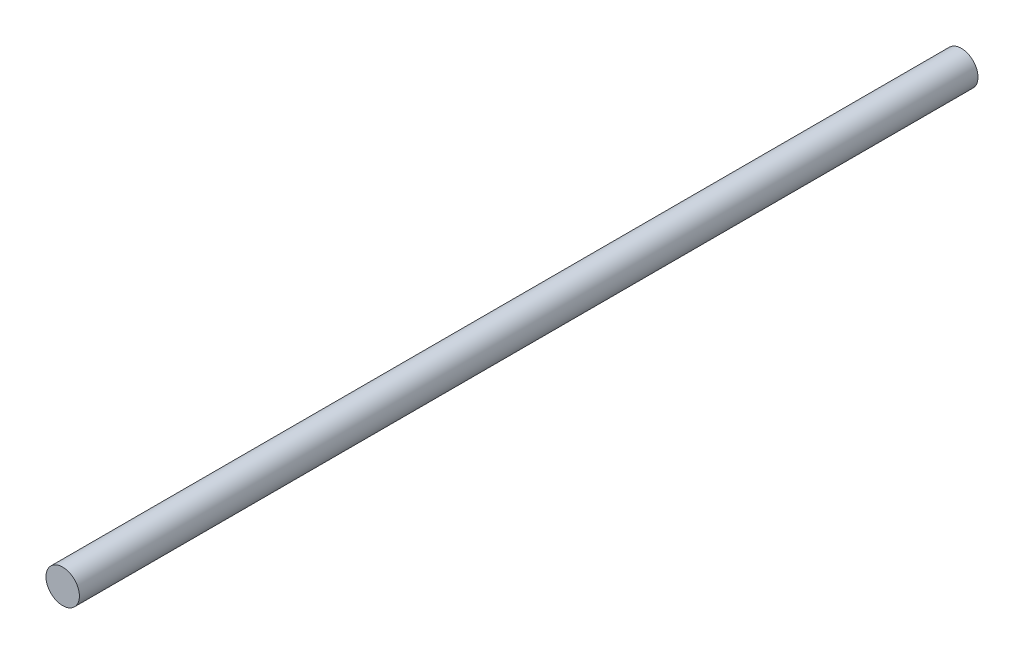
SolidWorks part; units mm, degrees
material "AISI 1020"
ref_plane "Front Plane" through (0, 0, 0) normal (0, 0, 1) x (1, 0, 0)
ref_plane "Top Plane" through (0, 0, 0) normal (0, 1, 0) x (1, 0, 0)
ref_plane "Right Plane" through (0, 0, 0) normal (1, 0, 0) x (0, 0, -1)
sketch "Sketch1" plane through (0, 0, 0) normal (0, 0, 1) x (1, 0, 0)
  circle A1 centre (0, 0) radius 4
  dimension "D1" = 8
extrude "Boss-Extrude1" add sketch "Sketch1" along normal blind 215
hole_wizard "M4x0.7 Tapped Hole2" positions "Sketch4" profile "Sketch5" tap size "M4x0.7" standard "ANSI Metric"
sketch "Sketch4" plane through (0, 0, 0) normal (0, 0, -1) x (-1, 0, 0)
  point P0 (0, 0)
sketch "Sketch5" plane through (0, 0, 0) normal (1, 0, 0) x (0, 1, 0)
  line L0 (0, 0) -> (0, 11.0914)
  line L1 (0, 11.0914) -> (1.65, 10.1)
  line L2 (1.65, 10.1) -> (1.65, 0)
  line L5 (1.65, 0) -> (0, 0)
  line L10 (0, 11.0914) -> (-1.65, 10.1) construction
  line L11 (0, -6.35) -> (0, 107.95) construction
  dimension "Tap Drill Dia." = 3.3
  dimension "Tap Drill Depth" = 10.1
  dimension "Drill Angle" = 118
cosmetic thread "Hole Thread2" parameters "D1"=8, "D2"=4
